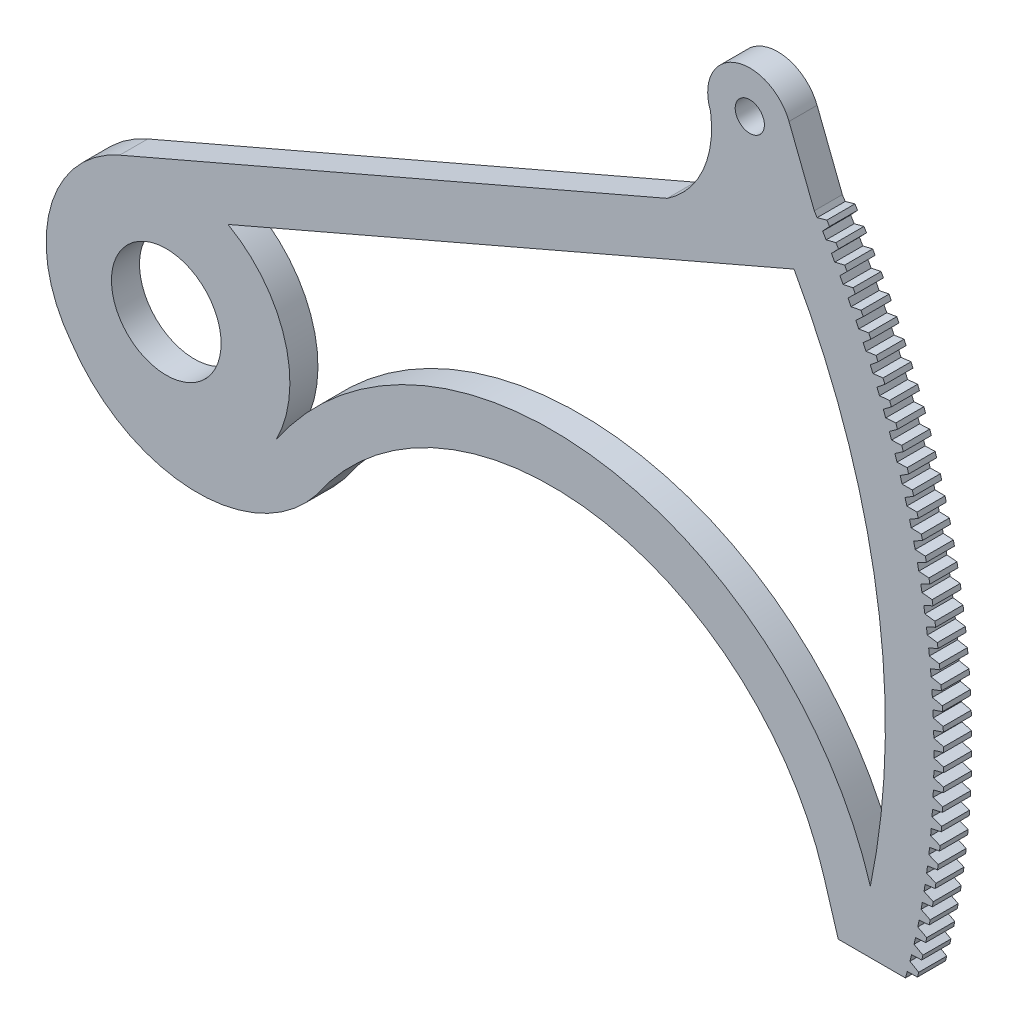
SolidWorks part; units mm, degrees
ref_plane "Front Plane" through (0, 0, 0) normal (0, 0, 1) x (1, 0, 0)
ref_plane "Top Plane" through (0, 0, 0) normal (0, 1, 0) x (1, 0, 0)
ref_plane "Right Plane" through (0, 0, 0) normal (1, 0, 0) x (0, 0, -1)
sketch "Sketch1" plane through (0, 0, 0) normal (0, 0, 1) x (1, 0, 0)
  line L0 (146.6332, 93.133) -> (140.913, 107.7805)
  line L1 (142.0413, 79.4124) -> (13.9816, 24.1366)
  line L2 (0, 0) -> (144.8412, 85.6593) construction
  line L3 (0, 0) -> (155.4658, 64.3961) construction
  line L4 (0.3914, 0.1345) -> (165.0416, 32.8288) construction
  line L5 (0, 0) -> (168.275, 0) construction
  line L6 (0, 0) -> (163.6549, -39.1607) construction
  line L230 (148.7673, -36.0992) -> (152.0541, -46.8963)
  line L231 (152.0541, -46.8963) -> (167.2596, -46.8963)
  line L232 (167.6694, -45.4093) -> (169.965, -45.371)
  line L233 (169.965, -45.371) -> (170.253, -44.2779)
  line L234 (170.253, -44.2779) -> (168.2739, -43.1152)
  line L235 (168.6483, -41.6268) -> (170.9424, -41.5369)
  line L236 (170.9424, -41.5369) -> (171.2058, -40.4376)
  line L237 (171.2058, -40.4376) -> (169.2011, -39.3197)
  line L238 (169.5418, -37.8233) -> (171.8334, -37.6818)
  line L239 (171.8334, -37.6818) -> (172.072, -36.5768)
  line L240 (172.072, -36.5768) -> (170.0426, -35.5043)
  line L241 (170.3496, -34.0006) -> (172.6374, -33.8076)
  line L242 (172.6374, -33.8076) -> (172.8511, -32.6976)
  line L243 (172.8511, -32.6976) -> (170.7981, -31.671)
  line L244 (171.0712, -30.1607) -> (173.3541, -29.9163)
  line L245 (173.3541, -29.9163) -> (173.5427, -28.8018)
  line L246 (173.5427, -28.8018) -> (171.4672, -27.8216)
  line L247 (171.7063, -26.3056) -> (173.9831, -26.0099)
  line L248 (173.9831, -26.0099) -> (174.1466, -24.8914)
  line L249 (174.1466, -24.8914) -> (172.0495, -23.9582)
  line L250 (172.2545, -22.4372) -> (174.524, -22.0903)
  line L251 (174.524, -22.0903) -> (174.6624, -20.9684)
  line L252 (174.6624, -20.9684) -> (172.5449, -20.0826)
  line L253 (172.7156, -18.5574) -> (174.9767, -18.1596)
  line L254 (174.9767, -18.1596) -> (175.0898, -17.0349)
  line L255 (175.0898, -17.0349) -> (172.9529, -16.1969)
  line L256 (173.0892, -14.6682) -> (175.3409, -14.2197)
  line L257 (175.3409, -14.2197) -> (175.4286, -13.0927)
  line L258 (175.4286, -13.0927) -> (173.2734, -12.3029)
  line L259 (173.3754, -10.7716) -> (175.6163, -10.2725)
  line L260 (175.6163, -10.2725) -> (175.6787, -9.1439)
  line L261 (175.6787, -9.1439) -> (173.5063, -8.4028)
  line L262 (173.5738, -6.8696) -> (175.803, -6.3202)
  line L263 (175.803, -6.3202) -> (175.8399, -5.1904)
  line L264 (175.8399, -5.1904) -> (173.6514, -4.4984)
  line L265 (173.6844, -2.964) -> (175.9006, -2.3647)
  line L266 (175.9006, -2.3647) -> (175.9122, -1.2344)
  line L267 (175.9122, -1.2344) -> (173.7086, -0.5917)
  line L268 (173.7071, 0.943) -> (175.9093, 1.592)
  line L269 (175.9093, 1.592) -> (175.8955, 2.7223)
  line L270 (175.8955, 2.7223) -> (173.678, 3.3152)
  line L271 (173.6419, 4.8495) -> (175.829, 5.5479)
  line L272 (175.829, 5.5479) -> (175.7897, 6.6776)
  line L273 (175.7897, 6.6776) -> (173.5595, 7.2205)
  line L274 (173.4889, 8.7536) -> (175.6598, 9.501)
  line L275 (175.6598, 9.501) -> (175.5951, 10.6296)
  line L276 (175.5951, 10.6296) -> (173.3532, 11.1222)
  line L277 (173.2482, 12.6533) -> (175.4017, 13.4493)
  line L278 (175.4017, 13.4493) -> (175.3116, 14.5761)
  line L279 (175.3116, 14.5761) -> (173.0592, 15.0182)
  line L280 (172.9198, 16.5465) -> (175.0548, 17.3908)
  line L281 (175.0548, 17.3908) -> (174.9394, 18.5153)
  line L282 (174.9394, 18.5153) -> (172.6777, 18.9066)
  line L283 (172.5039, 20.4314) -> (174.6194, 21.3235)
  line L284 (174.6194, 21.3235) -> (174.4788, 22.4451)
  line L285 (174.4788, 22.4451) -> (172.2088, 22.7854)
  line L286 (172.0008, 24.306) -> (174.0956, 25.2454)
  line L287 (174.0956, 25.2454) -> (173.9298, 26.3636)
  line L288 (173.9298, 26.3636) -> (171.6528, 26.6527)
  line L289 (171.4106, 28.1682) -> (173.4838, 29.1546)
  line L290 (173.4838, 29.1546) -> (173.2929, 30.2687)
  line L291 (173.2929, 30.2687) -> (171.0099, 30.5066)
  line L292 (170.7337, 32.0162) -> (172.7842, 33.0489)
  line L293 (172.7842, 33.0489) -> (172.5683, 34.1585)
  line L294 (172.5683, 34.1585) -> (170.2805, 34.345)
  line L295 (169.9705, 35.8481) -> (171.9972, 36.9266)
  line L296 (171.9972, 36.9266) -> (171.7564, 38.0311)
  line L297 (171.7564, 38.0311) -> (169.465, 38.166)
  line L298 (169.1212, 39.6617) -> (171.1232, 40.7856)
  line L299 (171.1232, 40.7856) -> (170.8576, 41.8843)
  line L300 (170.8576, 41.8843) -> (168.5638, 41.9677)
  line L301 (168.1864, 43.4553) -> (170.1627, 44.624)
  line L302 (170.1627, 44.624) -> (169.8724, 45.7164)
  line L303 (169.8724, 45.7164) -> (167.5773, 45.7482)
  line L304 (167.1665, 47.227) -> (169.116, 48.4397)
  line L305 (169.116, 48.4397) -> (168.8012, 49.5254)
  line L306 (168.8012, 49.5254) -> (166.506, 49.5056)
  line L307 (166.0621, 50.9747) -> (167.9838, 52.231)
  line L308 (167.9838, 52.231) -> (167.6447, 53.3093)
  line L309 (167.6447, 53.3093) -> (165.3504, 53.2379)
  line L310 (164.8736, 54.6967) -> (166.7666, 55.9959)
  line L311 (166.7666, 55.9959) -> (166.4033, 57.0663)
  line L312 (166.4033, 57.0663) -> (164.1113, 56.9433)
  line L313 (163.6018, 58.3909) -> (165.465, 59.7324)
  line L314 (165.465, 59.7324) -> (165.0778, 60.7944)
  line L315 (165.0778, 60.7944) -> (162.7891, 60.6198)
  line L316 (162.2471, 62.0557) -> (164.0797, 63.4387)
  line L317 (164.0797, 63.4387) -> (163.6687, 64.4917)
  line L318 (163.6687, 64.4917) -> (161.3845, 64.2657)
  line L319 (160.8104, 65.689) -> (162.6115, 67.1129)
  line L320 (162.6115, 67.1129) -> (162.1768, 68.1564)
  line L321 (162.1768, 68.1564) -> (159.8983, 67.8791)
  line L322 (159.2924, 69.2891) -> (161.0609, 70.7532)
  line L323 (161.0609, 70.7532) -> (160.6029, 71.7866)
  line L324 (160.6029, 71.7866) -> (158.3312, 71.4581)
  line L325 (157.6937, 72.8542) -> (159.4289, 74.3576)
  line L326 (159.4289, 74.3576) -> (158.9478, 75.3805)
  line L327 (158.9478, 75.3805) -> (156.684, 75.001)
  line L328 (156.0153, 76.3824) -> (157.7162, 77.9245)
  line L329 (157.7162, 77.9245) -> (157.2122, 78.9363)
  line L330 (157.2122, 78.9363) -> (154.9576, 78.506)
  line L331 (154.2579, 79.872) -> (155.9237, 81.4519)
  line L332 (155.9237, 81.4519) -> (155.3971, 82.4521)
  line L333 (155.3971, 82.4521) -> (153.1527, 81.9712)
  line L334 (152.4225, 83.3211) -> (154.0524, 84.9381)
  line L335 (154.0524, 84.9381) -> (153.5034, 85.9263)
  line L336 (153.5034, 85.9263) -> (151.2704, 85.395)
  line L337 (150.51, 86.7281) -> (152.1031, 88.3814)
  line L338 (152.1031, 88.3814) -> (151.5321, 89.3569)
  line L339 (151.5321, 89.3569) -> (149.3115, 88.7756)
  line L340 (148.5214, 90.0913) -> (150.0769, 91.7799)
  line L341 (150.0769, 91.7799) -> (149.484, 92.7424)
  line L342 (149.484, 92.7424) -> (147.2772, 92.1112)
  line L344 (113.3545, 78.9363) -> (-10.5395, 25.4586)
  arc A14 (159.3234, -32.8857) -> (142.0413, 79.4124) centre (0.3914, 0.1345) ccw
  arc A15 (159.3234, -32.8857) -> (24.7896, -12.7313) centre (87.2604, -54.8232) ccw
  arc A16 (24.7896, -12.7313) -> (13.9816, 24.1366) centre (0.3914, 0.1345) ccw
  circle A17 centre (0, 0) radius 12.4082
  circle A18 centre (0, 0) radius 168.275 construction
  circle A19 centre (132.0406, 104.3157) radius 3.302
  arc A20 (140.913, 107.7805) -> (123.162, 100.8665) centre (132.0406, 104.3157) ccw
  arc A21 (123.162, 100.8665) -> (113.3545, 78.9363) centre (100.9286, 97.6515) cw
  arc A82 (167.2596, -46.8963) -> (167.6694, -45.4093) centre (0, 0) ccw
  arc A83 (168.2739, -43.1152) -> (168.6483, -41.6268) centre (0, 0) ccw
  arc A84 (169.2011, -39.3197) -> (169.5418, -37.8233) centre (0, 0) ccw
  arc A85 (170.0426, -35.5043) -> (170.3496, -34.0006) centre (0, 0) ccw
  arc A86 (170.7981, -31.671) -> (171.0712, -30.1607) centre (0, 0) ccw
  arc A87 (171.4672, -27.8216) -> (171.7063, -26.3056) centre (0, 0) ccw
  arc A88 (172.0495, -23.9582) -> (172.2545, -22.4372) centre (0, 0) ccw
  arc A89 (172.5449, -20.0826) -> (172.7156, -18.5574) centre (0, 0) ccw
  arc A90 (172.9529, -16.1969) -> (173.0892, -14.6682) centre (0, 0) ccw
  arc A91 (173.2734, -12.3029) -> (173.3754, -10.7716) centre (0, 0) ccw
  arc A92 (173.5063, -8.4028) -> (173.5738, -6.8696) centre (0, 0) ccw
  arc A93 (173.6514, -4.4984) -> (173.6844, -2.964) centre (0, 0) ccw
  arc A94 (173.7086, -0.5917) -> (173.7071, 0.943) centre (0, 0) ccw
  arc A95 (173.678, 3.3152) -> (173.6419, 4.8495) centre (0, 0) ccw
  arc A96 (173.5595, 7.2205) -> (173.4889, 8.7536) centre (0, 0) ccw
  arc A97 (173.3532, 11.1222) -> (173.2482, 12.6533) centre (0, 0) ccw
  arc A98 (173.0592, 15.0182) -> (172.9198, 16.5465) centre (0, 0) ccw
  arc A99 (172.6777, 18.9066) -> (172.5039, 20.4314) centre (0, 0) ccw
  arc A100 (172.2088, 22.7854) -> (172.0008, 24.306) centre (0, 0) ccw
  arc A101 (171.6528, 26.6527) -> (171.4106, 28.1682) centre (0, 0) ccw
  arc A102 (171.0099, 30.5066) -> (170.7337, 32.0162) centre (0, 0) ccw
  arc A103 (170.2805, 34.345) -> (169.9705, 35.8481) centre (0, 0) ccw
  arc A104 (169.465, 38.166) -> (169.1212, 39.6617) centre (0, 0) ccw
  arc A105 (168.5638, 41.9677) -> (168.1864, 43.4553) centre (0, 0) ccw
  arc A106 (167.5773, 45.7482) -> (167.1665, 47.227) centre (0, 0) ccw
  arc A107 (166.506, 49.5056) -> (166.0621, 50.9747) centre (0, 0) ccw
  arc A108 (165.3504, 53.2379) -> (164.8736, 54.6967) centre (0, 0) ccw
  arc A109 (164.1113, 56.9433) -> (163.6018, 58.3909) centre (0, 0) ccw
  arc A110 (162.7891, 60.6198) -> (162.2471, 62.0557) centre (0, 0) ccw
  arc A111 (161.3845, 64.2657) -> (160.8104, 65.689) centre (0, 0) ccw
  arc A112 (159.8983, 67.8791) -> (159.2924, 69.2891) centre (0, 0) ccw
  arc A113 (158.3312, 71.4581) -> (157.6937, 72.8542) centre (0, 0) ccw
  arc A114 (156.684, 75.001) -> (156.0153, 76.3824) centre (0, 0) ccw
  arc A115 (154.9576, 78.506) -> (154.2579, 79.872) centre (0, 0) ccw
  arc A116 (153.1527, 81.9712) -> (152.4225, 83.3211) centre (0, 0) ccw
  arc A117 (151.2704, 85.395) -> (150.51, 86.7281) centre (0, 0) ccw
  arc A118 (149.3115, 88.7756) -> (148.5214, 90.0913) centre (0, 0) ccw
  arc A119 (147.2772, 92.1112) -> (146.6332, 93.133) centre (0, 0) ccw
  arc A120 (-10.5395, 25.4586) -> (-21.4871, -16.6622) centre (0.3914, 0.1345) ccw
  arc A121 (-21.4871, -16.6622) -> (33.9406, -18.8971) centre (7.0401, 2.3923) ccw
  arc A122 (148.7673, -36.0992) -> (33.9406, -18.8971) centre (87.2604, -54.8232) ccw
  dimension "D2" = 6.604
  dimension "D3" = 19.05
  dimension "D1" = 168.275
extrude "Boss-Extrude1" add sketch "Sketch1" along normal blind 6.35
